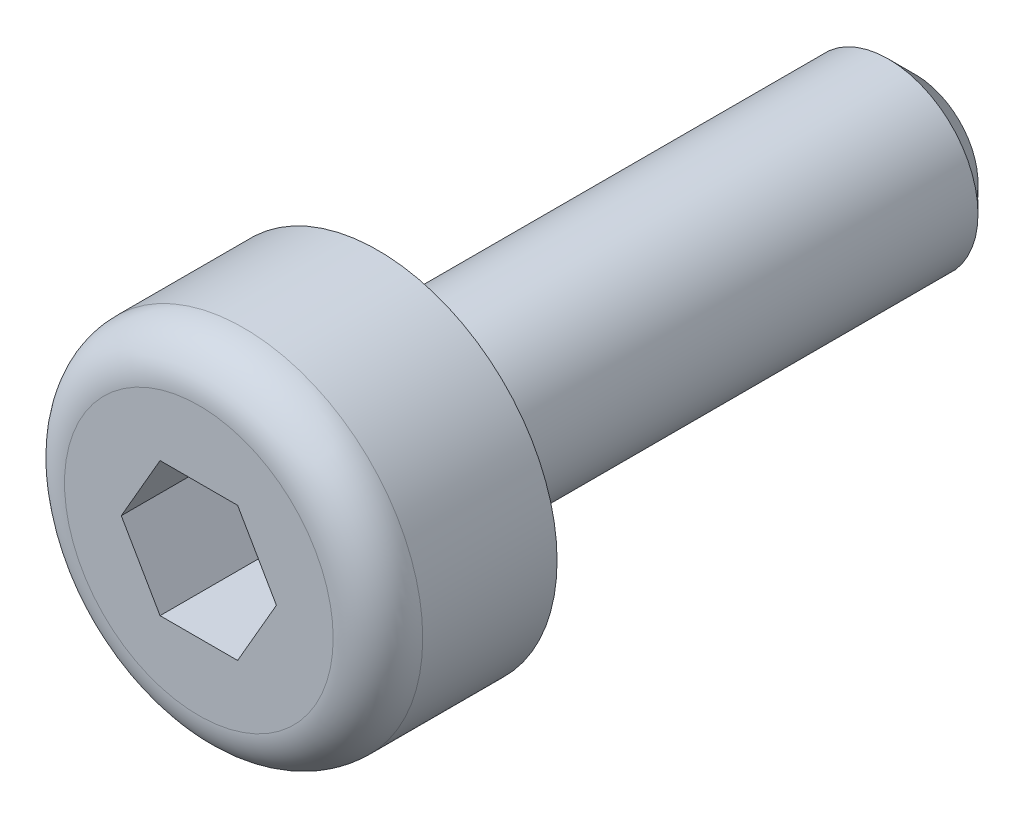
SolidWorks part; units mm, degrees
material "Ocel prostá uhlíková"
ref_plane "Přední rovina" through (0, 0, 0) normal (0, 0, 1) x (1, 0, 0)
ref_plane "Horní rovina" through (0, 0, 0) normal (0, 1, 0) x (1, 0, 0)
ref_plane "Pravá rovina" through (0, 0, 0) normal (1, 0, 0) x (0, 0, -1)
sketch "Skica1" plane through (0, 0, 0) normal (0, 0, 1) x (1, 0, 0)
  line L0 (0, 0) -> (-5.7735, 0) construction
  circle A0 centre (0, 0) radius 2
  dimension "D1" = 4
extrude "Přidat vysunutím1" add sketch "Skica1" along normal blind 2
sketch "Skica4" plane through (0, 0, 2) normal (0, 0, 1) x (1, 0, 0)
  line L1 (-0.866, 0) -> (-0.433, -0.75)
  line L2 (-0.433, -0.75) -> (0.433, -0.75)
  line L3 (0.433, -0.75) -> (0.866, 0)
  line L4 (0.866, 0) -> (0.433, 0.75)
  line L5 (0.433, 0.75) -> (-0.433, 0.75)
  line L6 (-0.433, 0.75) -> (-0.866, 0)
  line L7 (0, 0) -> (-5.7735, 0) construction
  circle A0 centre (0, 0) radius 0.75 construction
  dimension "D1" = 1.5
extrude "Odebrat vysunutím1" cut sketch "Skica4" against normal blind 2
sketch "Skica2" plane through (0, 0, 0) normal (0, 0, -1) x (-1, 0, 0)
  circle A0 centre (0, 0) radius 1
  dimension "D1" = 2
extrude "Přidat vysunutím2" add sketch "Skica2" along normal blind 6
chamfer "Zkosení1" distance 0.3 angle 45 1 edges at (-1, 0, -6)
fillet "Zaoblit1" radius 0.5 1 edges at (2, 0, 2)
